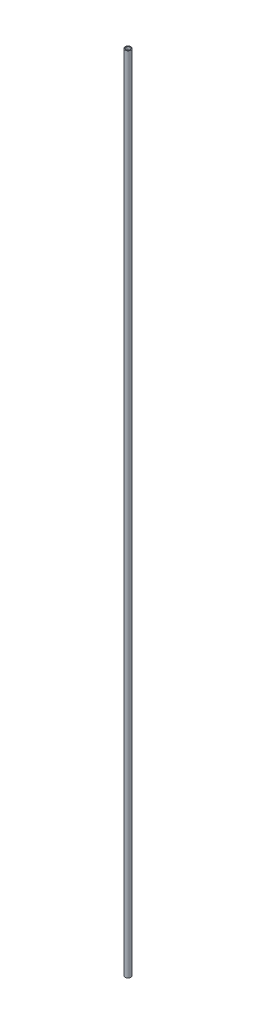
SolidWorks part; units mm, degrees
ref_plane "Front Plane" through (0, 0, 0) normal (0, 0, 1) x (1, 0, 0)
ref_plane "Top Plane" through (0, 0, 0) normal (0, 1, 0) x (1, 0, 0)
ref_plane "Right Plane" through (0, 0, 0) normal (1, 0, 0) x (0, 0, -1)
sketch "Sketch1" plane through (0, 0, 0) normal (0, 1, 0) x (1, 0, 0)
  circle A0 centre (0, 0) radius 0.0483
  circle A1 centre (0, 0) radius 0.066
  dimension "D1" = 0.0965
  dimension "D2" = 0.1321
extrude "Boss-Extrude1" add sketch "Sketch1" along normal blind 18
